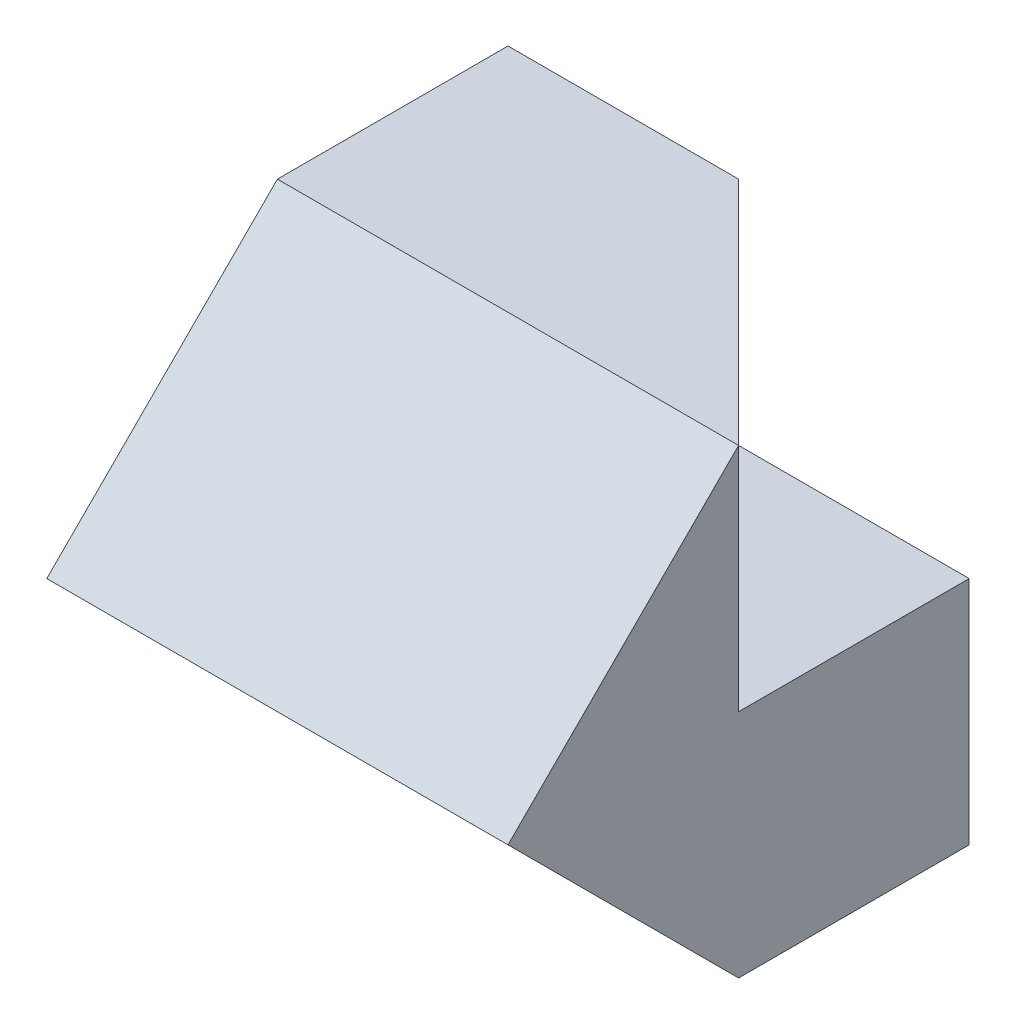
SolidWorks part; units mm, degrees
ref_plane "Front" through (0, 0, 0) normal (0, 0, 1) x (1, 0, 0)
ref_plane "Top" through (0, 0, 0) normal (0, 1, 0) x (1, 0, 0)
ref_plane "Right" through (0, 0, 0) normal (1, 0, 0) x (0, 0, -1)
sketch "Sketch1" plane through (0, 0, 0) normal (0, 0, 1) x (1, 0, 0)
  line L0 (0, 0) -> (0, 2)
  line L1 (0, 2) -> (-2, 2)
  line L2 (-2, 2) -> (-2, 4)
  line L3 (-2, 4) -> (2, 4)
  line L4 (2, 4) -> (2, 0)
  line L5 (2, 0) -> (0, 0)
  dimension "D1" = 2
  dimension "D2" = 2
  dimension "D3" = 2
  dimension "D4" = 4
extrude "Boss-Extrude1" add sketch "Sketch1" along normal blind 4
sketch "Sketch2" plane through (-2, 0, 0) normal (-1, 0, 0) x (0, 0, 1)
  line L0 (2, 4) -> (4, 2)
  line L1 (4, 4) -> (0, 4) construction
  line L2 (4, 2) -> (2, 0)
  line L3 (4, 0) -> (0, 0) construction
  line L4 (2, 0) -> (4, 0)
  line L5 (4, 0) -> (4, 4)
  line L6 (4, 4) -> (2, 4)
  line M3 (4, 2) -> (4, 4)
  line M4 (4, 4) -> (0, 4)
extrude "Cut-Extrude1" cut sketch "Sketch2" against normal blind 4 contours L0 M4 M3 | L4 L5 L2
sketch "Sketch3" plane through (0, 4, 0) normal (0, 1, 0) x (1, 0, 0)
  line L0 (2, -2) -> (0, 0)
  line L1 (2, 0) -> (-2, 0) construction
  line L2 (0, 0) -> (2, 0)
  line L3 (2, 0) -> (2, -2)
extrude "Cut-Extrude2" cut sketch "Sketch3" against normal blind 2
